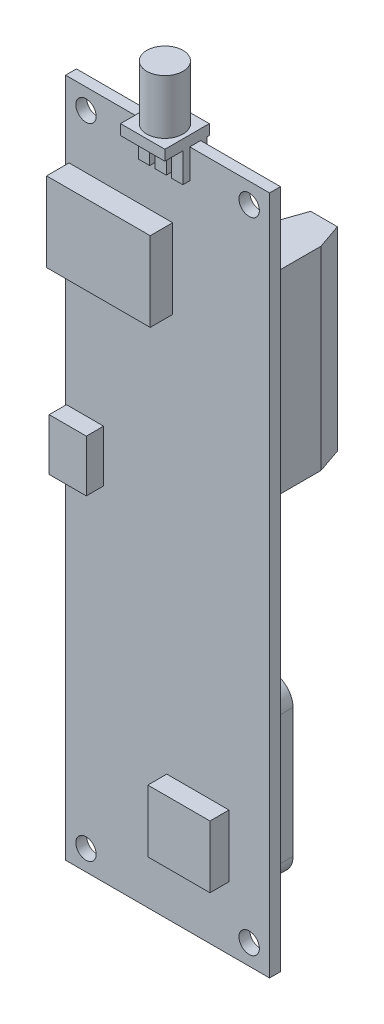
SolidWorks part; units mm, degrees
ref_plane "Front Plane" through (0, 0, 0) normal (0, 0, 1) x (1, 0, 0)
ref_plane "Top Plane" through (0, 0, 0) normal (0, 1, 0) x (1, 0, 0)
ref_plane "Right Plane" through (0, 0, 0) normal (1, 0, 0) x (0, 0, -1)
sketch "Sketch3" plane through (0, 0, 0) normal (1, 0, 0) x (0, 0, -1)
  line L0 (0, 0) -> (-1.6002, 0)
  line L1 (-1.6002, 0) -> (-1.6002, -100)
  line L2 (0, 0) -> (0, -100)
  line L3 (-1.6002, -100) -> (0, -100)
  point P5 (-0.8001, -100)
  dimension "D1" = 1.6002
  dimension "D2" = 100
extrude "Boss-Extrude1" add sketch "Sketch3" along normal blind 30
sketch "Sketch5" plane through (0, 0, 1.6002) normal (0, 0, 1) x (1, 0, 0)
  line L0 (30, -100) -> (0, -100) construction
  line L1 (30, 0) -> (30, -100) construction
  line L2 (30, 0) -> (0, 0) construction
  line L3 (0, 0) -> (0, -100) construction
  circle A0 centre (27, -3) radius 1.5
  circle A1 centre (3, -3) radius 1.5
  circle A2 centre (3, -97) radius 1.5
  circle A3 centre (27, -97) radius 1.5
  dimension "D1" = 3
  dimension "D2" = 3
  dimension "D3" = 3
  dimension "D5" = 3
  dimension "D6" = 3
  dimension "D7" = 3
  dimension "D8" = 3
  dimension "D4" = 3
  dimension "D9" = 3
extrude "Screw-Holes" cut sketch "Sketch5" against normal blind 13.39
sketch "Sketch7" plane through (0, 0, 0) normal (0, 0, -1) x (-1, 0, 0)
  line L0 (-30, 0) -> (-19.9356, 0) construction
  line L1 (-29.746, -10.8204) -> (-23.269, -10.8204)
  line L2 (-29.746, -10.8204) -> (-29.746, -39.3954)
  line L3 (-29.746, -39.3954) -> (-23.269, -39.3954)
  line L4 (-23.269, -10.8204) -> (-23.269, -39.3954)
  line L5 (-30, -100) -> (-30, 0) construction
  dimension "D1" = 28.575
  dimension "D2" = 6.477
  dimension "D3" = 10.8204
  dimension "D4" = 0.254
extrude "Boss-Extrude2" add sketch "Sketch7" along normal blind 9.906
sketch "Sketch8" plane through (0, -10.8204, 0) normal (0, 1, 0) x (1, 0, 0)
  line L0 (28.476, 9.906) -> (29.746, 6.223)
  line L1 (23.269, 9.906) -> (29.746, 9.906) construction
  line L2 (29.746, 9.906) -> (29.746, 0) construction
  line L3 (26.5075, 9.906) -> (26.5075, 5.0057) construction
  line L4 (28.476, 9.906) -> (29.746, 9.906)
  line L5 (29.746, 9.906) -> (29.746, 6.223)
  line L6 (23.269, 9.906) -> (23.269, 6.223)
  line L7 (24.539, 9.906) -> (23.269, 9.906)
  line L8 (24.539, 9.906) -> (23.269, 6.223)
  dimension "D1" = 3.683
  dimension "D2" = 1.27
extrude "Cut-Extrude1" cut sketch "Sketch8" against normal up to next
sketch "Sketch9" plane through (0, 0, 0) normal (0, 0, -1) x (-1, 0, 0)
  line L0 (-30, 0) -> (0, 0) construction
  line L1 (0, -100) -> (0, 0) construction
  circle A0 centre (-12.3825, -34.29) radius 6.0325
  dimension "D1" = 12.065
  dimension "D2" = 34.29
  dimension "D3" = 12.3825
extrude "Boss-Extrude3" add sketch "Sketch9" along normal blind 6.35
fillet "Fillet1" radius 0.762 1 edges at (12.3825, -28.2575, -6.35)
sketch "Sketch10" plane through (0, 0, 0) normal (0, 0, -1) x (-1, 0, 0)
  line L1 (-27.5349, -66.6752) -> (-2.4651, -66.6752)
  line L2 (-27.5349, -66.6752) -> (-27.5349, -91.745)
  line L3 (-27.5349, -91.745) -> (-2.4651, -91.745)
  line L4 (-2.4651, -66.6752) -> (-2.4651, -91.745)
  line L5 (-27.5349, -66.6752) -> (-2.4651, -91.745) construction
  line L6 (-27.5349, -91.745) -> (-2.4651, -66.6752) construction
  line L9 (-30, -100) -> (0, -100) construction
  point P0 (-15, -79.2101)
  dimension "D1" = 25.0698
  dimension "D2" = 8.255
extrude "Boss-Extrude4" add sketch "Sketch10" along normal blind 4.318
fillet "Fillet2" radius 3.048 4 edges at (2.4651, -66.6752, -2.159) (2.4651, -91.745, -2.159) (27.5349, -66.6752, -2.159) (27.5349, -91.745, -2.159)
sketch "Sketch11" plane through (0, 0, -4.318) normal (0, 0, -1) x (-1, 0, 0)
  line L0 (-15, -91.745) -> (-15, -66.6752) construction
  line L1 (-24.4869, -91.745) -> (-5.5131, -91.745) construction
  line L2 (-5.5131, -66.6752) -> (-24.4869, -66.6752) construction
  line L4 (-24.779, -69.4311) -> (-5.221, -69.4311)
  line L5 (-24.779, -69.4311) -> (-24.779, -88.9891)
  line L6 (-24.779, -88.9891) -> (-5.221, -88.9891)
  line L7 (-5.221, -69.4311) -> (-5.221, -88.9891)
  line L8 (-24.779, -69.4311) -> (-5.221, -88.9891) construction
  line L9 (-24.779, -88.9891) -> (-5.221, -69.4311) construction
  point P6 (-15, -79.2101)
  dimension "D1" = 19.558
extrude "Sticker" add sketch "Sketch11" along normal blind 0.0254
sketch "Sketch12" plane through (0, 0, 1.6002) normal (0, 0, 1) x (1, 0, 0)
  line L0 (30, 0) -> (0, 0) construction
  line L1 (0.508, -10.922) -> (15.748, -10.922)
  line L2 (0.508, -10.922) -> (0.508, -22.606)
  line L3 (0.508, -22.606) -> (15.748, -22.606)
  line L4 (15.748, -10.922) -> (15.748, -22.606)
  line L5 (0, 0) -> (0, -100) construction
  dimension "D1" = 15.24
  dimension "D2" = 11.684
  dimension "D3" = 10.922
  dimension "D4" = 0.508
extrude "Big chip" add sketch "Sketch12" along normal blind 3.302
sketch "Sketch13" plane through (0, 0, 1.6002) normal (0, 0, 1) x (1, 0, 0)
  line L0 (30, 0) -> (30, -100) construction
  line L1 (14.887, -81.585) -> (24.031, -81.585)
  line L2 (14.887, -81.585) -> (14.887, -90.729)
  line L3 (14.887, -90.729) -> (24.031, -90.729)
  line L4 (24.031, -81.585) -> (24.031, -90.729)
  line L5 (30, -100) -> (0, -100) construction
  dimension "D1" = 9.144
  dimension "D2" = 5.969
  dimension "D3" = 9.271
extrude "ublox chip" add sketch "Sketch13" along normal blind 2.794
sketch "Sketch14" plane through (0, 0, 0) normal (0, 1, 0) x (1, 0, 0)
  line L0 (15, 0) -> (15, -1.6002) construction
  line L1 (30, 0) -> (0, 0) construction
  line L2 (30, -1.6002) -> (0, -1.6002) construction
  line L4 (11.7361, 1.27) -> (18.2639, 1.27)
  line L5 (11.7361, 1.27) -> (11.7361, -5.2578)
  line L6 (11.7361, -5.2578) -> (18.2639, -5.2578)
  line L7 (18.2639, 1.27) -> (18.2639, -5.2578)
  line L8 (11.7361, 1.27) -> (18.2639, -5.2578) construction
  line L9 (11.7361, -5.2578) -> (18.2639, 1.27) construction
  point P6 (15, -1.9939)
  dimension "D1" = 6.5278
  dimension "D2" = 1.27
extrude "Boss-Extrude8" add sketch "Sketch14" along normal blind 1.524
sketch "Sketch15" plane through (0, 1.524, 0) normal (0, 1, 0) x (1, 0, 0)
  line L0 (15, 1.27) -> (15, -5.2578) construction
  line L1 (18.2639, 1.27) -> (11.7361, 1.27) construction
  line L2 (11.7361, -5.2578) -> (18.2639, -5.2578) construction
  circle A0 centre (15, -1.9939) radius 2.667
  dimension "D1" = 5.334
extrude "Boss-Extrude9" add sketch "Sketch15" along normal blind 8.001
sketch "Sketch17" plane through (0, 0, 0) normal (0, -1, 0) x (1, 0, 0)
  line L0 (14.1745, 1.6002) -> (14.1745, 2.6162)
  line L1 (11.7361, 1.6002) -> (13.3871, 1.6002)
  line L2 (11.7361, 1.6002) -> (11.7361, 2.6162)
  line L3 (11.7361, 2.6162) -> (13.3871, 2.6162)
  line L4 (13.3871, 1.6002) -> (13.3871, 2.6162)
  line L5 (14.1745, 1.6002) -> (15.8255, 1.6002)
  line L6 (15.8255, 1.6002) -> (15.8255, 2.6162)
  line L7 (14.1745, 2.6162) -> (15.8255, 2.6162)
  line L8 (16.6129, 1.6002) -> (16.6129, 2.6162)
  line L9 (16.6129, 1.6002) -> (18.2639, 1.6002)
  line L10 (18.2639, 1.6002) -> (18.2639, 2.6162)
  line L11 (16.6129, 2.6162) -> (18.2639, 2.6162)
  dimension "D1" = 1.651
  dimension "D2" = 1.016
  dimension "D3" = 3
extrude "Boss-Extrude10" add sketch "Sketch17" along normal blind 4.318
sketch "Sketch18" plane through (0, 0, 0) normal (0, -1, 0) x (1, 0, 0)
  line L0 (15, -1.27) -> (15, 0) construction
  line L1 (11.7361, 0) -> (13.3871, 0)
  line L2 (11.7361, 0) -> (11.7361, -0.9652)
  line L3 (11.7361, -0.9652) -> (13.3871, -0.9652)
  line L4 (13.3871, 0) -> (13.3871, -0.9652)
  line L5 (18.2639, -1.27) -> (11.7361, -1.27) construction
  line L6 (18.2639, 0) -> (11.7361, 0) construction
  line L7 (18.2639, -0.9652) -> (16.6129, -0.9652)
  line L8 (16.6129, 0) -> (16.6129, -0.9652)
  line L9 (18.2639, 0) -> (16.6129, 0)
  line L10 (18.2639, 0) -> (18.2639, -0.9652)
  dimension "D1" = 1.651
  dimension "D2" = 0.9652
extrude "Boss-Extrude11" add sketch "Sketch18" along normal blind 4.318
sketch "Sketch19" plane through (0, 0, 1.6002) normal (0, 0, 1) x (1, 0, 0)
  line L1 (0.127, -41.91) -> (5.588, -41.91)
  line L2 (0.127, -41.91) -> (0.127, -49.53)
  line L3 (0.127, -49.53) -> (5.588, -49.53)
  line L4 (5.588, -41.91) -> (5.588, -49.53)
  line L5 (0, 0) -> (0, -100) construction
  line L6 (11.7361, 0) -> (0, 0) construction
  dimension "D1" = 7.62
  dimension "D2" = 5.461
  dimension "D3" = 0.127
  dimension "D4" = 41.91
extrude "USB connector" add sketch "Sketch19" along normal blind 2.54
equation "\"D3@Sketch9\"=0.25+0.475/2"
